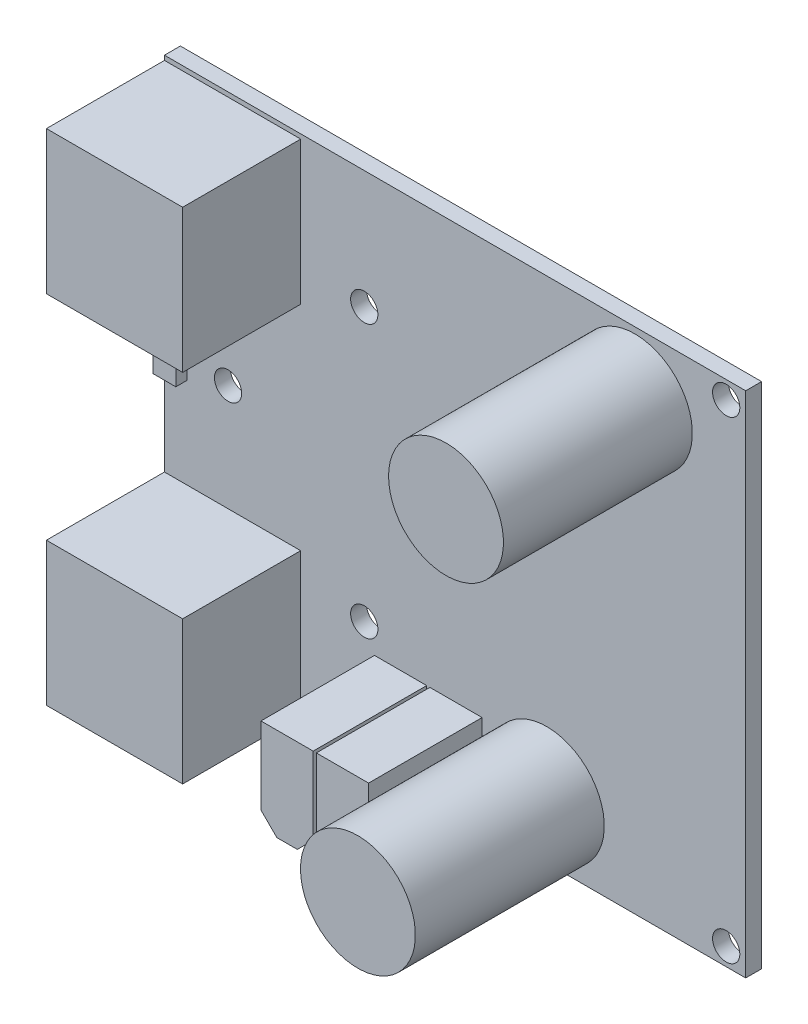
SolidWorks part; units mm, degrees
ref_plane "Front Plane" through (0, 0, 0) normal (0, 0, 1) x (1, 0, 0)
ref_plane "Top Plane" through (0, 0, 0) normal (0, 1, 0) x (1, 0, 0)
ref_plane "Right Plane" through (0, 0, 0) normal (1, 0, 0) x (0, 0, -1)
ref_plane "Plane1" through (0, 0, 9.525) normal (0, 0, -1) x (-1, 0, 0)
sketch "Sketch1" plane through (0, 0, 9.525) normal (0, 0, -1) x (-1, 0, 0)
  line L0 (-102.325, 28) -> (-102.325, -28)
  line L1 (-102.325, -28) -> (-38.325, -28)
  line L2 (-38.325, -28) -> (-38.325, 28)
  line L3 (-38.325, 28) -> (-102.325, 28)
extrude "Boss-Extrude1" add sketch "Sketch1" against normal blind 1.75
sketch "Sketch2" plane through (0, 0, 11.275) normal (0, 0, 1) x (1, 0, 0)
  line L0 (42.425, 10.2) -> (42.425, 2.2)
  line L1 (42.425, 2.2) -> (36.825, 2.2)
  line L2 (36.825, 2.2) -> (36.825, 10.2)
  line L3 (36.825, 10.2) -> (42.425, 10.2)
extrude "Boss-Extrude2" add sketch "Sketch2" along normal blind 3.25
sketch "Sketch3" plane through (0, 0, 11.275) normal (0, 0, 1) x (1, 0, 0)
  line L0 (61.45, -17.675) -> (67.2, -17.675)
  line L1 (67.2, -17.675) -> (67.2, -26.175)
  line L2 (67.2, -26.175) -> (65.45, -27.925)
  line L3 (65.45, -27.925) -> (63.2, -27.925)
  line L4 (63.2, -27.925) -> (61.45, -26.175)
  line L5 (61.45, -26.175) -> (61.45, -17.675)
extrude "Boss-Extrude3" add sketch "Sketch3" along normal blind 12.5
sketch "Sketch4" plane through (0, 0, 11.275) normal (0, 0, 1) x (1, 0, 0)
  line L0 (38.325, -1.75) -> (38.325, 1.5)
  line L1 (38.325, 1.5) -> (40.825, 1.5)
  line L2 (40.825, 1.5) -> (40.825, -1.75)
  line L3 (40.825, -1.75) -> (38.325, -1.75)
extrude "Boss-Extrude4" add sketch "Sketch4" along normal blind 1.25
sketch "Sketch5" plane through (0, 0, 11.275) normal (0, 0, 1) x (1, 0, 0)
  line L0 (53.325, -11.75) -> (53.325, -27.5)
  line L1 (53.325, -27.5) -> (38.325, -27.5)
  line L2 (38.325, -27.5) -> (38.325, -11.75)
  line L3 (38.325, -11.75) -> (53.325, -11.75)
extrude "Boss-Extrude5" add sketch "Sketch5" along normal blind 13
sketch "Sketch6" plane through (0, 0, 11.275) normal (0, 0, 1) x (1, 0, 0)
  line L0 (53.325, 27.5) -> (53.325, 11.75)
  line L1 (53.325, 11.75) -> (38.325, 11.75)
  line L2 (38.325, 11.75) -> (38.325, 27.5)
  line L3 (38.325, 27.5) -> (53.325, 27.5)
extrude "Boss-Extrude6" add sketch "Sketch6" along normal blind 13
sketch "Sketch7" plane through (0, 0, 11.275) normal (0, 0, 1) x (1, 0, 0)
  line L0 (67.55, -17.675) -> (73.3, -17.675)
  line L1 (73.3, -17.675) -> (73.3, -26.175)
  line L2 (73.3, -26.175) -> (71.55, -27.925)
  line L3 (71.55, -27.925) -> (69.3, -27.925)
  line L4 (69.3, -27.925) -> (67.55, -26.175)
  line L5 (67.55, -26.175) -> (67.55, -17.675)
extrude "Boss-Extrude7" add sketch "Sketch7" along normal blind 12.5
sketch "Sketch8" plane through (0, 0, 9.525) normal (0, 0, -1) x (-1, 0, 0)
  line L0 (-63.575, 3.25) -> (-57.075, 3.25)
  line L1 (-57.075, 3.25) -> (-57.075, -3.25)
  line L2 (-57.075, -3.25) -> (-63.575, -3.25)
  line L3 (-63.575, -3.25) -> (-63.575, 3.25)
extrude "Boss-Extrude8" add sketch "Sketch8" along normal blind 1.9
ref_plane "Plane2" through (0, -21.3, 0) normal (0, -1, 0) x (1, 0, 0)
sketch "Sketch9" plane through (0, -21.3, 0) normal (0, -1, 0) x (1, 0, 0)
  line L0 (86.75, 32.075) -> (80.425, 32.075)
  line L1 (80.425, 32.075) -> (80.425, 11.275)
  line L2 (80.425, 11.275) -> (86.75, 11.275)
  line L3 (86.75, 11.275) -> (86.75, 32.075)
  line L4 (80.425, 32.075) -> (80.425, 11.275) construction
revolve "Revolve1" add sketch "Sketch9" angle 360 about L4
ref_plane "Plane3" through (0, 21, 0) normal (0, -1, 0) x (1, 0, 0)
sketch "Sketch10" plane through (0, 21, 0) normal (0, -1, 0) x (1, 0, 0)
  line L0 (96.45, 32.075) -> (90.125, 32.075)
  line L1 (90.125, 32.075) -> (90.125, 11.275)
  line L2 (90.125, 11.275) -> (96.45, 11.275)
  line L3 (96.45, 11.275) -> (96.45, 32.075)
  line L4 (90.125, 32.075) -> (90.125, 11.275) construction
revolve "Revolve2" add sketch "Sketch10" angle 360 about L4
hole_wizard "#3 Clearance Hole1" positions "Sketch12" profile "Sketch11" hole size "#3" standard "ANSI Inch"
sketch "Sketch12" plane through (0, 0, 9.525) normal (0, 0, -1) x (-1, 0, 0)
  point P0 (-45.325, 0)
  point P1 (-60.325, 15)
  point P2 (-75.325, 0)
  point P3 (-60.325, -15)
  point P4 (-100.175, 26.05)
  point P5 (-100.175, -26.05)
sketch "Sketch11" plane through (45.325, 0, 9.525) normal (1, 0, 0) x (0, 1, 0)
  line L0 (0, 0) -> (0, 22.55)
  line L1 (0, 22.55) -> (1.5, 22.55)
  line L2 (1.5, 22.55) -> (1.5, 0)
  line L5 (1.5, 0) -> (0, 0)
  line L11 (0, -6.35) -> (0, 107.95) construction
  dimension "Thru Hole Dia." = 3
  dimension "Thru Hole Depth" = 22.55
